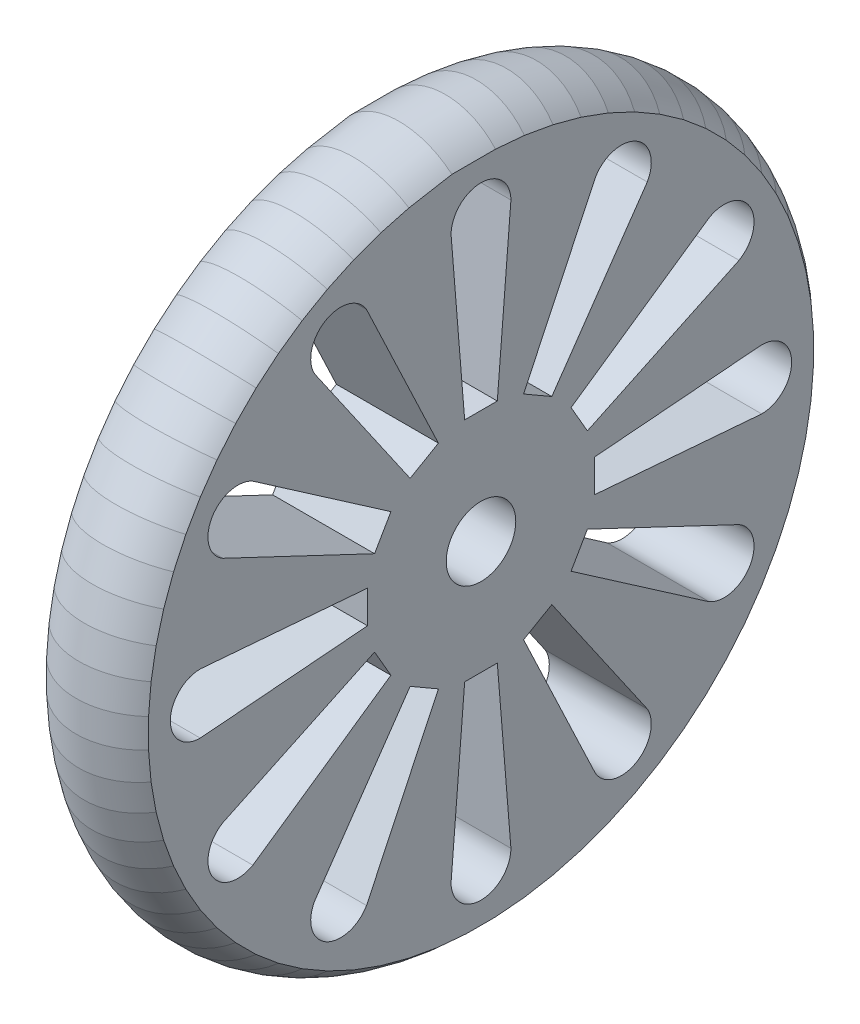
SolidWorks part; units mm, degrees
ref_plane "Front Plane" through (0, 0, 0) normal (0, 0, 1) x (1, 0, 0)
ref_plane "Top Plane" through (0, 0, 0) normal (0, 1, 0) x (1, 0, 0)
ref_plane "Right Plane" through (0, 0, 0) normal (1, 0, 0) x (0, 0, -1)
sketch "Sketch1" plane through (0, 0, 0) normal (1, 0, 0) x (0, 0, -1)
  circle A0 centre (0, 0) radius 20
  circle A1 centre (0, 0) radius 1.705
  dimension "D1" = 3.41
  dimension "D2" = 40
extrude "Boss-Extrude1" add sketch "Sketch1" along normal blind 5
sketch "Sketch2" plane through (0, 0, 0) normal (1, 0, 0) x (0, 0, -1)
  line L0 (0, 0) -> (0, 12.5028) construction
  line L4 (1.4673, 13.7644) -> (0.8004, 5.5623)
  line L5 (-0.8004, 5.5623) -> (0.8004, 5.5623)
  line L6 (-1.4673, 13.7644) -> (-0.8004, 5.5623)
  arc A11 (-1.4673, 13.7644) -> (1.4673, 13.7644) centre (0, 13.7644) cw
  point P13 (0, 5.5623)
extrude "Cut-Extrude1" cut sketch "Sketch2" along normal blind 8
pattern_circular "CirPattern1" count 12 every 30 about axis through (0, 0, 0) along (1, 0, 0) of "Cut-Extrude1"
sketch "Sketch6" plane through (0, 0, 0) normal (0, 0, 1) x (1, 0, 0)
  line L4 (0, 20) -> (0, -20) construction
  line L6 (5, -20) -> (5, 20) construction
  line L7 (0, 16.3) -> (0, 20)
  line L8 (0, 20) -> (5, 20)
  line L9 (5, 20) -> (5, 16.3)
  arc A4 (0, 16.3) -> (5, 16.3) centre (2.5, 13.8505) cw
  dimension "D3" = 3.5
  dimension "D1" = 3.7
  dimension "D2" = 3.7
extrude "Cut-Extrude2" cut sketch "Sketch6" against normal mid plane 5
pattern_circular "CirPattern2" count 71 every 5 about axis through (5, 0, 0) along (-1, 0, 0) of "Cut-Extrude2"
